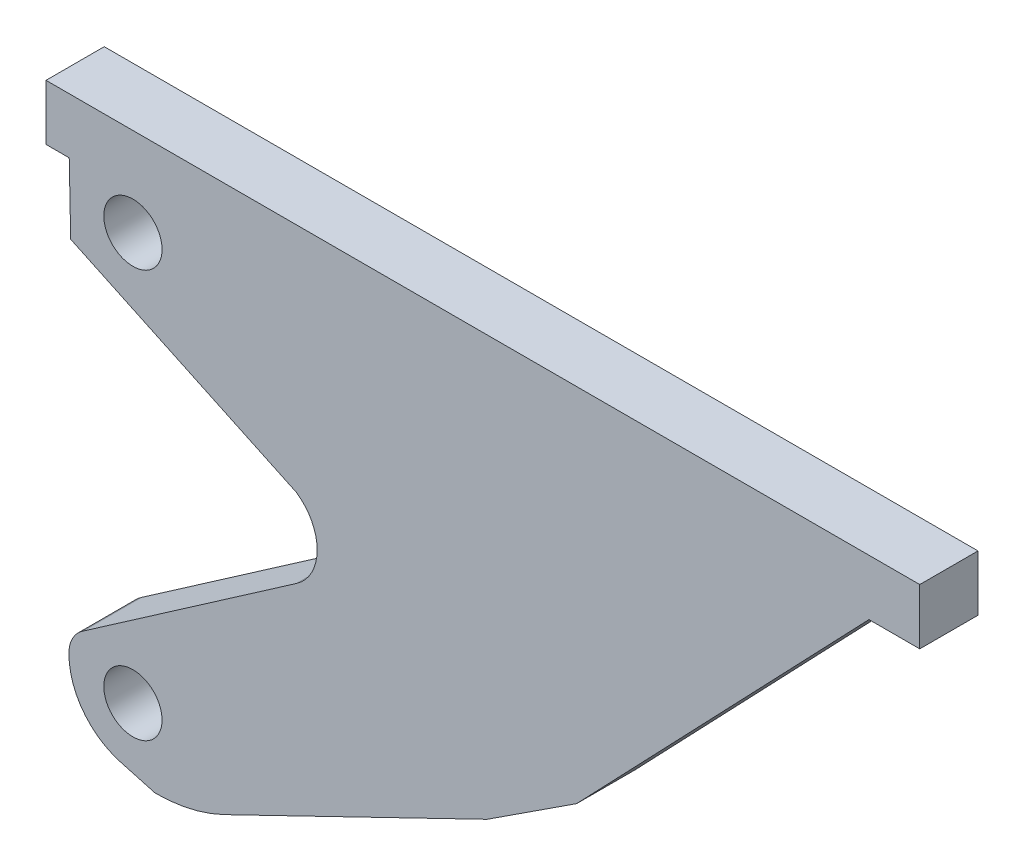
SolidWorks part; units mm, degrees
ref_plane "Front Plane" through (0, 0, 0) normal (0, 0, 1) x (1, 0, 0)
ref_plane "Top Plane" through (0, 0, 0) normal (0, 1, 0) x (1, 0, 0)
ref_plane "Right Plane" through (0, 0, 0) normal (1, 0, 0) x (0, 0, -1)
sketch "Szkic1" [suppressed] plane through (0, 0, 0) normal (0, 0, 1) x (1, 0, 0)
  line L5 (0, 0) -> (300, 0)
  line L6 (0, 0) -> (0, 200)
  line L7 (0, 200) -> (300, 200)
  line L8 (300, 0) -> (300, 200)
  circle A0 centre (30, 170) radius 10
  circle A1 centre (30, 30) radius 10
  dimension "D6" = 20
  dimension "D1" = 300
  dimension "D2" = 200
  dimension "D3" = 30
  dimension "D4" = 30
  dimension "D5" = 30
extrude "Dodanie-wyciągnięcie1" [suppressed] add sketch "Szkic1" along normal blind 20
other "Grafika1"
other "Grafika (Zamknięta) -1"
sketch "Szkic3" plane through (0, 0, 0) normal (0, 0, 1) x (1, 0, 0)
  line L0 (12.6781, 42.4888) -> (86.0364, 93.3441)
  line L1 (86.0364, 120.3556) -> (8.4811, 156.8986)
  line L2 (8.4811, 156.8986) -> (7.9766, 180.8634)
  line L3 (7.9766, 180.8634) -> (0, 180.8634)
  line L4 (0, 180.8634) -> (0, 199.9302)
  line L5 (0, 199.9302) -> (300, 200)
  line L6 (300, 200) -> (300, 180.8634)
  line L7 (300, 180.8634) -> (282.5642, 180.8634)
  line L8 (282.5642, 180.8634) -> (182.1801, 75.9351)
  line L9 (182.1801, 75.9351) -> (151.4393, 55.9075)
  line L10 (151.4393, 55.9075) -> (61.1681, 12.1674)
  line L11 (37.4689, 6.7283) -> (25.5748, 10.0205)
  arc A0 (86.0364, 93.3441) -> (86.0364, 120.3556) centre (76.6736, 106.8499) ccw
  arc A1 (61.1681, 12.1674) -> (37.4689, 6.7283) centre (37.4689, 61.0781) cw
  arc A2 (25.5748, 10.0205) -> (7.8812, 33.7966) centre (32.0142, 33.2842) cw
  arc A3 (7.8812, 33.7966) -> (12.6781, 42.4888) centre (18.5661, 33.5697) cw
  circle A4 centre (29.8456, 29.6228) radius 10
  circle A5 centre (29.8456, 169.5416) radius 10
  point P38 (0, 0)
  dimension "D1" = 20
extrude "Dodanie-wyciągnięcie2" add sketch "Szkic3" along normal blind 20
